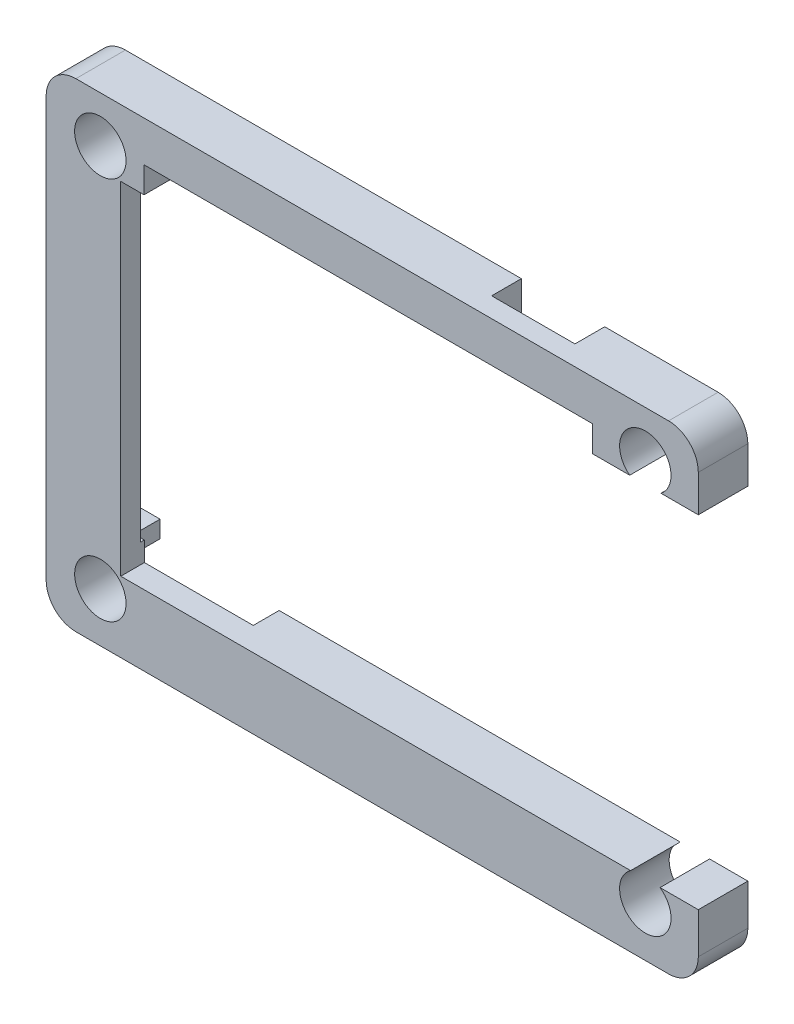
SolidWorks part; units mm, degrees
ref_plane "前视基准面" through (0, 0, 0) normal (0, 0, 1) x (1, 0, 0)
ref_plane "上视基准面" through (0, 0, 0) normal (0, 1, 0) x (1, 0, 0)
ref_plane "右视基准面" through (0, 0, 0) normal (1, 0, 0) x (0, 0, -1)
sketch "草图1" plane through (0, 0, 0) normal (0, 0, 1) x (1, 0, 0)
  line L1 (-30.5854, 20.7927) -> (24.4146, 20.7927) construction
  line L2 (-30.5854, 20.7927) -> (-30.5854, -17.9073) construction
  line L3 (-30.5854, -17.9073) -> (24.4146, -17.9073) construction
  line L4 (24.4146, 20.7927) -> (24.4146, -17.9073) construction
  line L5 (-33.0534, 25.4449) -> (26.7614, 25.4449)
  line L6 (-36.0534, 22.4449) -> (-36.0534, -19.897)
  line L7 (-33.0534, -22.897) -> (26.7614, -22.897)
  line L8 (29.7614, 22.4449) -> (29.7614, -19.897)
  line L9 (-28.5256, 18.7306) -> (22.2295, 18.7306)
  line L10 (-28.5256, 18.7306) -> (-28.5256, -15.7785)
  line L11 (-28.5256, -15.7785) -> (22.2295, -15.7785)
  line L12 (22.2295, 18.7306) -> (22.2295, -15.7785)
  circle A0 centre (-30.5854, 20.7927) radius 2.5947
  circle A1 centre (24.4146, 20.7927) radius 2.5947
  circle A2 centre (-30.5854, -17.9073) radius 2.5947
  circle A3 centre (24.4146, -17.9073) radius 2.5947
  arc A4 (26.7614, -22.897) -> (29.7614, -19.897) centre (26.7614, -19.897) ccw
  arc A5 (26.7614, 25.4449) -> (29.7614, 22.4449) centre (26.7614, 22.4449) cw
  arc A6 (-36.0534, -19.897) -> (-33.0534, -22.897) centre (-33.0534, -19.897) ccw
  arc A7 (-33.0534, 25.4449) -> (-36.0534, 22.4449) centre (-33.0534, 22.4449) ccw
  dimension "D1" = 55
  dimension "D3" = 3
  dimension "D2" = 38.7
extrude "凸台-拉伸1" add sketch "草图1" along normal blind 5
sketch "草图2" plane through (0, -22.897, 0) normal (0, -1, 0) x (1, 0, 0)
  line L0 (-33.0534, 0) -> (26.7614, 0) construction
  line L1 (-29.5563, 2.6142) -> (-17.5392, 2.6142)
  line L2 (-29.5563, 2.6142) -> (-29.5563, 0)
  line L3 (-29.5563, 0) -> (-17.5392, 0)
  line L4 (-17.5392, 2.6142) -> (-17.5392, 0)
extrude "切除-拉伸1" cut sketch "草图2" against normal blind 10
sketch "草图3" plane through (0, 0, 0) normal (0, 0, -1) x (-1, 0, 0)
  line L0 (36.0534, 22.4449) -> (36.0534, -19.897) construction
  line L1 (36.0534, 17.1804) -> (28.5256, 17.1804)
  line L2 (36.0534, 17.1804) -> (36.0534, -13.8046)
  line L3 (36.0534, -13.8046) -> (28.5256, -13.8046)
  line L4 (28.5256, 17.1804) -> (28.5256, -13.8046)
  line L5 (28.5256, 18.7306) -> (28.5256, -12.897) construction
extrude "切除-拉伸2" cut sketch "草图3" against normal blind 3
sketch "草图4" plane through (0, 0, 5) normal (0, 0, 1) x (1, 0, 0)
  line L1 (22.2295, 18.7306) -> (34.0478, 18.7306)
  line L2 (22.2295, 18.7306) -> (22.2295, -15.7785)
  line L3 (22.2295, -15.7785) -> (34.0478, -15.7785)
  line L4 (34.0478, 18.7306) -> (34.0478, -15.7785)
extrude "切除-拉伸3" cut sketch "草图4" against normal blind 10
sketch "草图5" plane through (0, 0, 0) normal (0, 0, -1) x (-1, 0, 0)
  line L1 (-6.9064, 13.6795) -> (-15.3138, 13.6795)
  line L2 (-6.9064, 13.6795) -> (-6.9064, 27.433)
  line L3 (-6.9064, 27.433) -> (-15.3138, 27.433)
  line L4 (-15.3138, 13.6795) -> (-15.3138, 27.433)
extrude "切除-拉伸4" cut sketch "草图5" against normal blind 3
sketch "草图6" plane through (0, 0, 0) normal (0, 0, -1) x (-1, 0, 0)
  line L1 (26.1751, 17.3349) -> (-19.0606, 17.3349)
  line L2 (26.1751, 17.3349) -> (26.1751, 21.3559)
  line L3 (26.1751, 21.3559) -> (-19.0606, 21.3559)
  line L4 (-19.0606, 17.3349) -> (-19.0606, 21.3559)
extrude "切除-拉伸5" cut sketch "草图6" against normal blind 10
